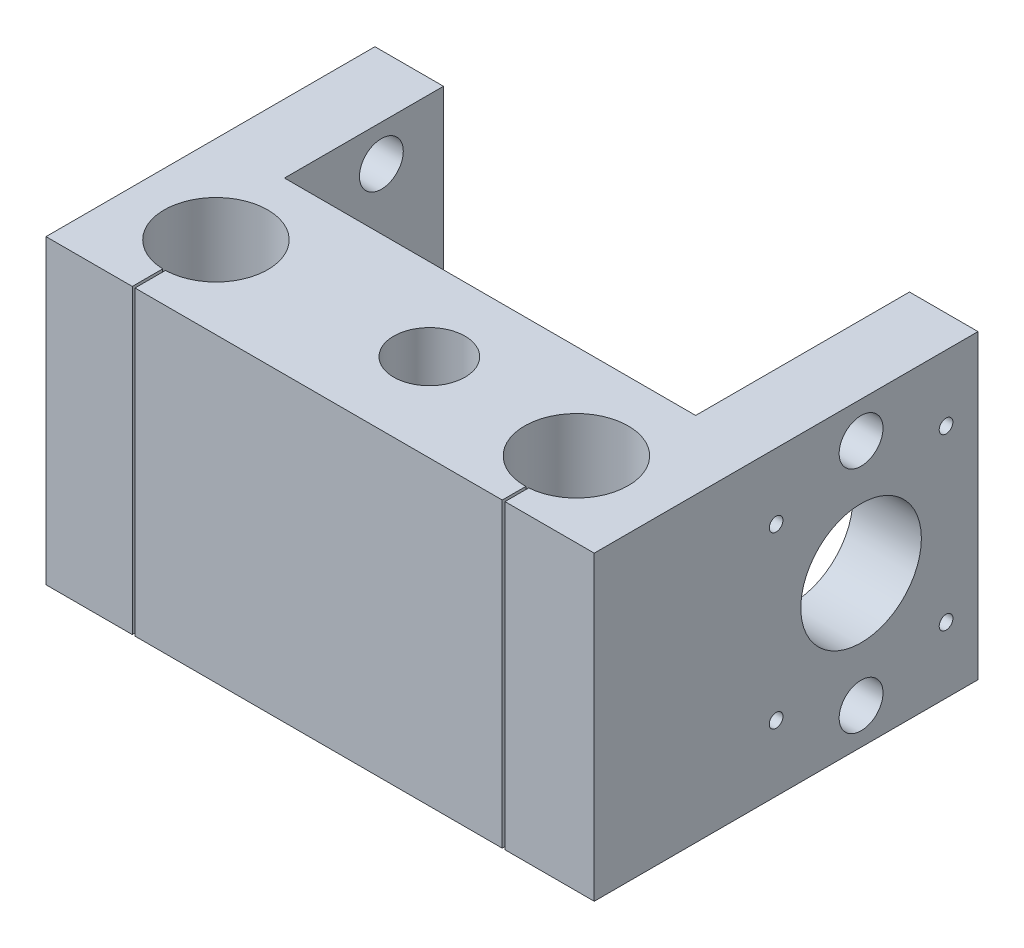
SolidWorks part; units mm, degrees
ref_plane "Front Plane" through (0, 0, 0) normal (0, 0, 1) x (1, 0, 0)
ref_plane "Top Plane" through (0, 0, 0) normal (0, 1, 0) x (1, 0, 0)
ref_plane "Right Plane" through (0, 0, 0) normal (1, 0, 0) x (0, 0, -1)
sketch "Sketch1" plane through (0, 0, 0) normal (0, 1, 0) x (1, 0, 0)
  line L1 (-50, 35) -> (50, 35)
  line L2 (-50, 35) -> (-50, -35)
  line L3 (-50, -35) -> (50, -35)
  line L4 (50, 35) -> (50, -35)
  line L5 (-50, 35) -> (50, -35) construction
  line L6 (-50, -35) -> (50, 35) construction
  line L7 (-37.5, 35) -> (37.5, 35)
  line L8 (-37.5, 35) -> (-37.5, -4)
  line L9 (-37.5, -4) -> (37.5, -4)
  line L10 (37.5, 35) -> (37.5, -4)
  point P0 (0, 0)
  dimension "D1" = 100
  dimension "D2" = 70
  dimension "D3" = 12.5
  dimension "D4" = 12.5
  dimension "D5" = 31
extrude "Boss-Extrude1" add sketch "Sketch1" along normal blind 55 contours L1 L10 L9 L8 L2 L3 L4
sketch "Sketch2" plane through (0, 0, -35) normal (0, 0, -1) x (-1, 0, 0)
  line L1 (37.5, 0) -> (50, 0)
  line L2 (37.5, 0) -> (37.5, 55)
  line L3 (37.5, 55) -> (50, 55)
  line L4 (50, 0) -> (50, 55)
extrude "Cut-Extrude1" cut sketch "Sketch2" against normal blind 10
sketch "Sketch4" plane through (0, 55, 0) normal (0, 1, 0) x (1, 0, 0)
  line L0 (50, -35) -> (50, -21.25) construction
  line L1 (50, 35) -> (50, -35) construction
  line L2 (50, -21.25) -> (33, -21.25) construction
  circle A0 centre (33, -21.25) radius 9.45
  dimension "D3" = 18.9
  dimension "D1" = 13.75
  dimension "D2" = 17
extrude "Cut-Extrude2" cut sketch "Sketch4" against normal through all
sketch "Sketch5" plane through (0, 55, 0) normal (0, 1, 0) x (1, 0, 0)
  circle A0 centre (-34, -20) radius 9.45
  dimension "D1" = 18.9
extrude "Cut-Extrude3" cut sketch "Sketch5" against normal through all
sketch "Sketch7" plane through (50, 0, 0) normal (1, 0, 0) x (0, 0, -1)
  circle A0 centre (29.1731, 12) radius 1.25
  circle A1 centre (-1.8269, 12) radius 1.25
  circle A2 centre (-1.8269, 43) radius 1.25
  circle A3 centre (29.1731, 43) radius 1.25
extrude "Cut-Extrude5" cut sketch "Sketch7" against normal blind 35
sketch "Sketch8" plane through (50, 0, 0) normal (1, 0, 0) x (0, 0, -1)
  circle A0 centre (13.6731, 27.5) radius 11
extrude "Cut-Extrude6" cut sketch "Sketch8" against normal blind 35
sketch "Sketch9" plane through (50, 0, 0) normal (1, 0, 0) x (0, 0, -1)
  line L0 (30.5731, 48.4) -> (-3.2269, 48.4) construction
  line L1 (-3.2269, 6.6) -> (30.5731, 6.6) construction
  circle A0 centre (13.6731, 48.4) radius 4
  circle A1 centre (13.6731, 6.6) radius 4
  dimension "D1" = 8
  dimension "D2" = 8
extrude "Cut-Extrude7" cut sketch "Sketch9" against normal through all both and the other way through all
sketch "Sketch11" plane through (-37.5, 0, 0) normal (1, 0, 0) x (0, 0, -1)
  circle A0 centre (13.6731, 27.5) radius 4
  dimension "D1" = 8
extrude "Cut-Extrude8" cut sketch "Sketch11" against normal blind 100
sketch "Sketch12" plane through (0, 0, 0) normal (0, -1, 0) x (1, 0, 0)
  line L5 (33.2215, 28.5714) -> (33.7215, 28.5714)
  line L6 (33.2215, 28.5714) -> (33.2215, 36.0091)
  line L7 (33.2215, 36.0091) -> (33.7215, 36.0091)
  line L8 (33.7215, 28.5714) -> (33.7215, 36.0091)
  line L9 (-34.2641, 27.0281) -> (-33.7641, 27.0281)
  line L10 (-34.2641, 27.0281) -> (-34.2641, 36.1661)
  line L11 (-34.2641, 36.1661) -> (-33.7641, 36.1661)
  line L12 (-33.7641, 27.0281) -> (-33.7641, 36.1661)
  dimension "D1" = 0.5
  dimension "D2" = 0.5
extrude "Cut-Extrude9" cut sketch "Sketch12" against normal through all contours L10 L9 L12 L11 | L6 L5 L8 L7
sketch "Sketch13" plane through (0, 55, 0) normal (0, 1, 0) x (1, 0, 0)
  circle A0 centre (3.9254, -19) radius 6.5
  dimension "D1" = 13
extrude "Cut-Extrude10" cut sketch "Sketch13" against normal through all
